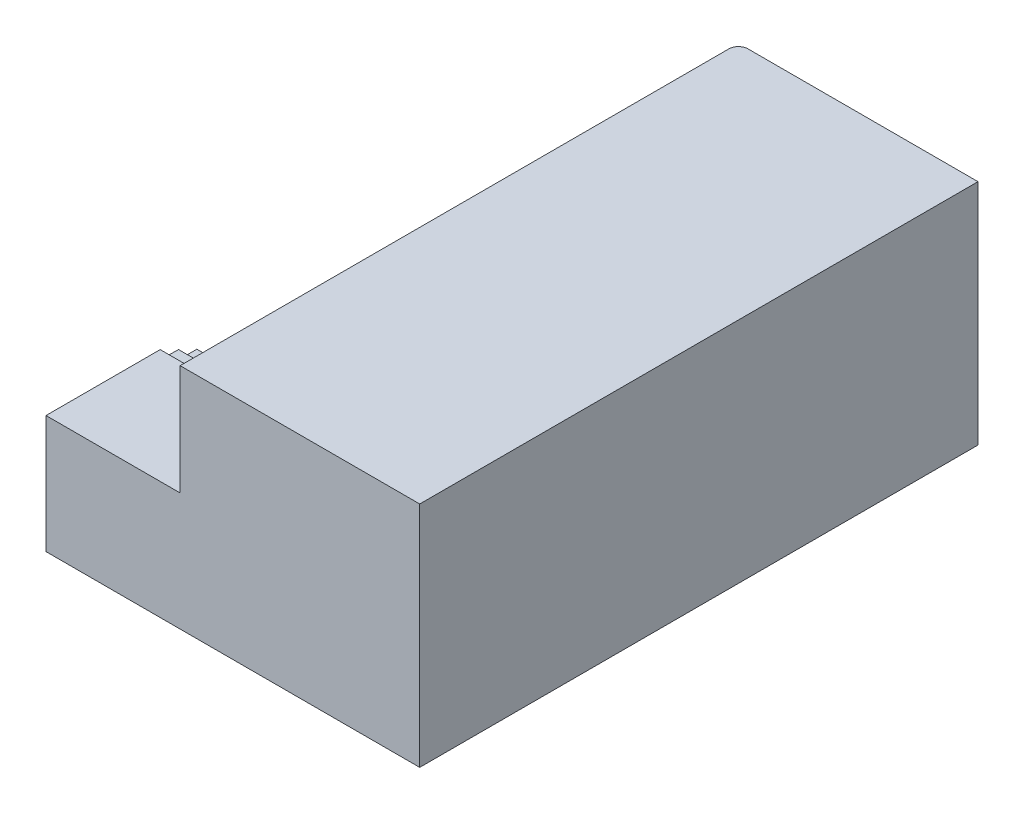
SolidWorks part; units mm, degrees
ref_plane "Front Plane" through (0, 0, 0) normal (0, 0, 1) x (1, 0, 0)
ref_plane "Top Plane" through (0, 0, 0) normal (0, 1, 0) x (1, 0, 0)
ref_plane "Right Plane" through (0, 0, 0) normal (1, 0, 0) x (0, 0, -1)
sketch "Sketch1" plane through (0, 0, 0) normal (1, 0, 0) x (0, 0, -1)
  line L0 (-98.3, 73.7131) -> (-60, 73.7131)
  line L1 (-60, 73.7131) -> (-60, 55.2131)
  line L2 (-60, 55.2131) -> (-21.7039, 54.669)
  line L7 (-21.7039, 54.669) -> (-21.7039, 36.169)
  line L8 (-21.7039, 36.169) -> (16.5961, 36.169)
  line L9 (16.5961, 36.169) -> (16.5961, 17.669)
  line L10 (16.5961, 17.669) -> (54.8961, 17.669)
  line L11 (54.8961, 17.669) -> (54.8961, -0.831)
  line L12 (54.8961, -0.831) -> (93.1961, -0.831)
  line L13 (93.1961, -0.831) -> (93.1961, -19.331)
  line L14 (93.1961, -19.331) -> (131.4961, -19.331)
  line L15 (131.4961, -19.331) -> (131.4961, -37.831)
  line L16 (131.4961, -37.831) -> (169.7961, -37.831)
  line L17 (169.7961, -37.831) -> (169.7961, -56.331)
  line L18 (169.7961, -56.331) -> (208.0961, -56.331)
  line L19 (208.0961, -56.331) -> (208.0961, -74.831)
  line L20 (208.0961, -74.831) -> (246.3961, -74.831)
  line L21 (246.3961, -74.831) -> (246.3961, -93.331)
  line L22 (246.3961, -93.331) -> (284.6961, -93.331)
  line L23 (284.6961, -93.331) -> (284.6961, -111.831)
  line L24 (284.6961, -111.831) -> (322.9961, -111.831)
  line L25 (322.9961, -111.831) -> (322.9961, -130.331)
  line L26 (322.9961, -130.331) -> (361.2961, -130.331)
  line L27 (361.2961, -130.331) -> (361.2961, -148.831)
  line L28 (361.2961, -148.831) -> (399.5961, -148.831)
  line L29 (399.5961, -148.831) -> (399.5961, -167.331)
  line L30 (-98.3, 73.7131) -> (-98.3, -167.331)
  line L31 (-98.3, 73.7131) -> (399.5961, 73.7131) construction
  line L32 (-98.3, 73.7131) -> (-98.3, -167.331) construction
  line L33 (-98.3, -167.331) -> (399.5961, -167.331) construction
  line L34 (399.5961, 73.7131) -> (399.5961, -167.331) construction
  line L35 (-98.3, -167.331) -> (399.5961, -167.331)
  point P4 (0, 0)
  dimension "D3" = 38.3
  dimension "D4" = 18.5
extrude "Boss-Extrude1" add sketch "Sketch1" against normal blind 280
sketch "Sketch2" plane through (0, 0, 98.3) normal (0, 0, 1) x (1, 0, 0)
  line L1 (-280, -167.331) -> (0, -167.331)
  line L2 (-280, -167.331) -> (-280, -172.331)
  line L3 (-280, -172.331) -> (0, -172.331)
  line L4 (0, -167.331) -> (0, -172.331)
  dimension "D1" = 5
extrude "Boss-Extrude2" add sketch "Sketch2" against normal up to surface (497.8961 mm away) up to face at (-140, -158.081, -399.5961)
sketch "Sketch3" plane through (0, 0, 98.3) normal (0, 0, 1) x (1, 0, 0)
  line L1 (-280, 73.7131) -> (0, 73.7131)
  line L2 (-280, 73.7131) -> (-280, -172.331)
  line L3 (-280, -172.331) -> (0, -172.331)
  line L4 (0, 73.7131) -> (0, -172.331)
extrude "Boss-Extrude3" add sketch "Sketch3" along normal blind 200
sketch "Sketch4" plane through (0, 0, -399.5961) normal (0, 0, -1) x (-1, 0, 0)
  line L0 (280, -172.331) -> (280, -148.831) construction
  line L1 (0, -172.331) -> (280, -172.331)
  line L2 (0, -172.331) -> (0, -167.6057)
  line L3 (0, -167.6057) -> (280, -167.6057)
  line L4 (280, -172.331) -> (280, -167.6057)
extrude "Boss-Extrude4" add sketch "Sketch4" along normal blind 467.31
sketch "Sketch5" plane through (0, 0, 0) normal (1, 0, 0) x (0, 0, -1)
  line L5 (-298.3, -172.331) -> (866.9061, -172.331)
  line L6 (-298.3, -172.331) -> (-298.3, 303.811)
  line L7 (-298.3, 303.811) -> (866.9061, 303.811)
  line L8 (866.9061, -172.331) -> (866.9061, 303.811)
extrude "Boss-Extrude5" add sketch "Sketch5" along normal blind 500
fillet "Fillet1" radius 20 1 edges at (0, 68.1027, -866.9061)
